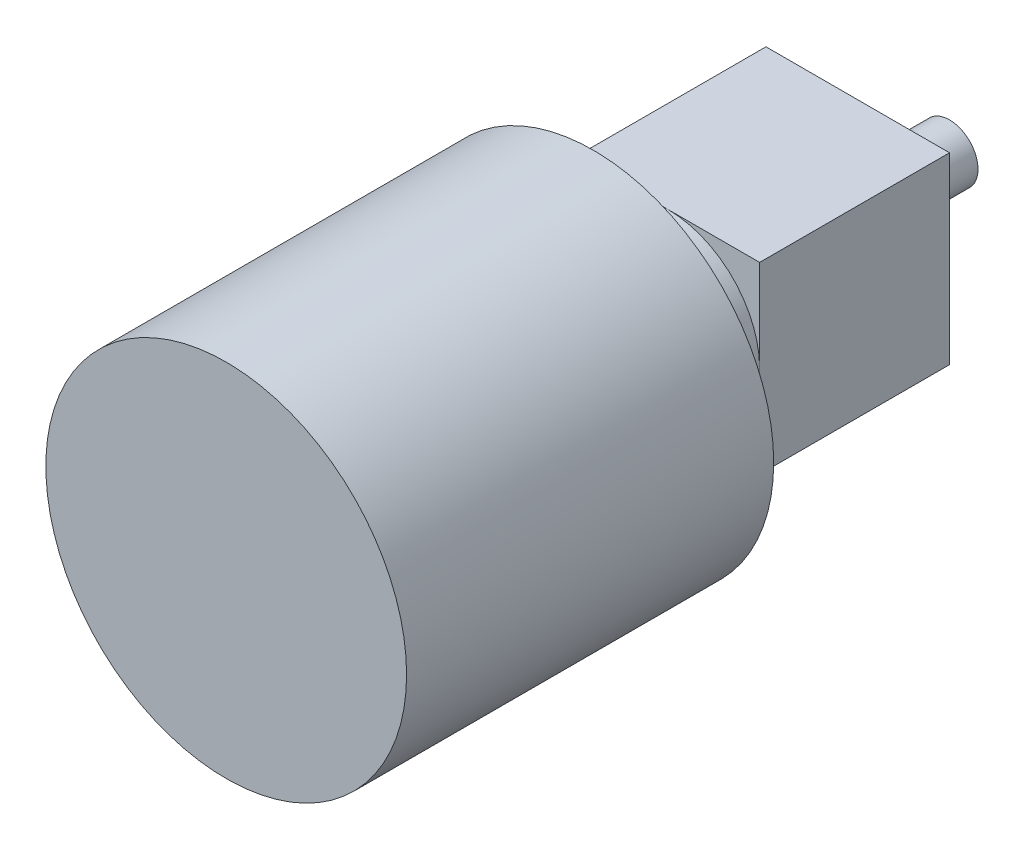
SolidWorks part; units mm, degrees
ref_plane "Front Plane" through (0, 0, 0) normal (0, 0, 1) x (1, 0, 0)
ref_plane "Top Plane" through (0, 0, 0) normal (0, 1, 0) x (1, 0, 0)
ref_plane "Right Plane" through (0, 0, 0) normal (1, 0, 0) x (0, 0, -1)
sketch "Sketch1" plane through (0, 0, 0) normal (0, 1, 0) x (1, 0, 0)
  line L1 (14.5, -15) -> (-14.5, -15)
  line L2 (14.5, -15) -> (14.5, 15)
  line L3 (14.5, 15) -> (-14.5, 15)
  line L4 (-14.5, -15) -> (-14.5, 15)
  line L5 (14.5, -15) -> (-14.5, 15) construction
  line L6 (14.5, 15) -> (-14.5, -15) construction
  point P0 (0, 0)
  dimension "D1" = 29
  dimension "D2" = 30
extrude "Boss-Extrude1" add sketch "Sketch1" along normal blind 29
sketch "Sketch2" plane through (0, 0, 15) normal (0, 0, 1) x (1, 0, 0)
  line L0 (-14.5, 29) -> (-14.5, 0) construction
  circle A0 centre (0, 14.5) radius 14.5
  point P4 (-14.5, 14.5)
  dimension "D1" = 29
extrude "Boss-Extrude2" add sketch "Sketch2" along normal blind 11.78
sketch "Sketch3" plane through (0, 0, 0) normal (0, -1, 0) x (1, 0, 0)
  line L0 (-14.5, 15) -> (0, 15) construction
  circle A0 centre (-10, 12) radius 1.2
  circle A1 centre (10, 12) radius 1.2
  circle A2 centre (0, -11.5) radius 1.2
  dimension "D1" = 20
  dimension "D4" = 2.4
  dimension "D2" = 3
  dimension "D3" = 10
  dimension "D5" = 26.5
extrude "Cut-Extrude1" cut sketch "Sketch3" against normal blind 2.5
sketch "Sketch4" plane through (0, 0, -15) normal (0, 0, -1) x (-1, 0, 0)
  line L0 (-14.5, 29) -> (-14.5, 0) construction
  line L1 (-14.5, 29) -> (14.5, 29) construction
  circle A0 centre (-8.5, 23) radius 4.5
  dimension "D1" = 9
  dimension "D2" = 6
  dimension "D3" = 6
extrude "Boss-Extrude3" add sketch "Sketch4" along normal blind 6
sketch "Sketch5" plane through (0, 0, 26.78) normal (0, 0, 1) x (1, 0, 0)
  circle A0 centre (0, 14.5) radius 28.5
  circle A1 centre (0, 14.5) radius 14.5 construction
  dimension "D1" = 57
extrude "Boss-Extrude4" add sketch "Sketch5" along normal blind 58
